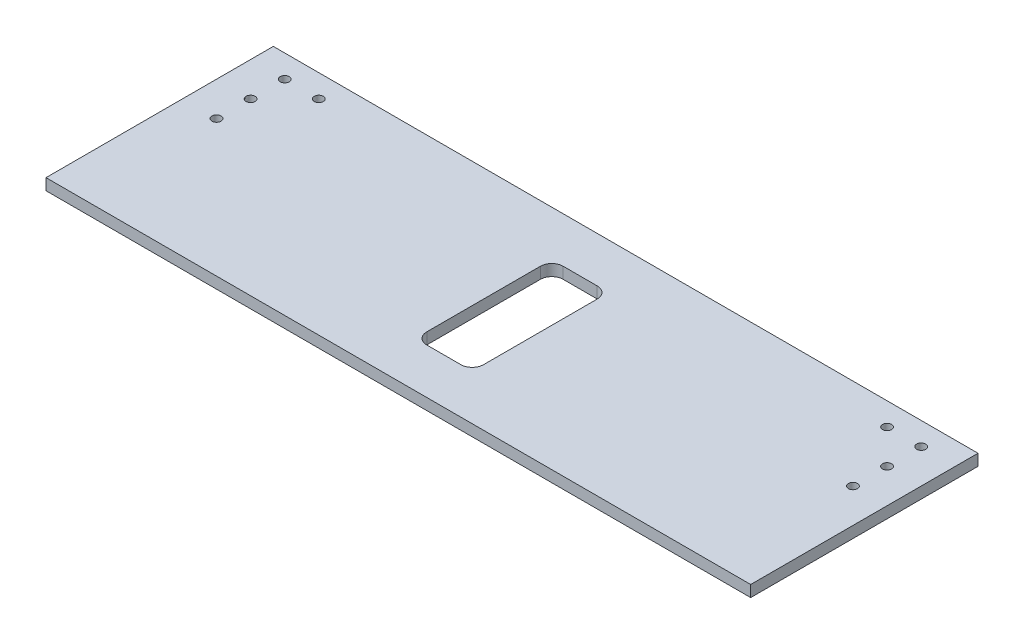
SolidWorks part; units mm, degrees
ref_plane "前视基准面" through (0, 0, 0) normal (0, 0, 1) x (1, 0, 0)
ref_plane "上视基准面" through (0, 0, 0) normal (0, 1, 0) x (1, 0, 0)
ref_plane "右视基准面" through (0, 0, 0) normal (1, 0, 0) x (0, 0, -1)
sketch "Sketch1" plane through (0, 0, 0) normal (0, 1, 0) x (1, 0, 0)
  line L0 (0, 50) -> (0, 97.5) construction
  line L1 (-155, 50) -> (155, 50)
  line L2 (-155, 50) -> (-155, -50)
  line L3 (-155, -50) -> (155, -50)
  line L4 (155, 50) -> (155, -50)
  line L5 (-155, 50) -> (155, -50) construction
  line L6 (-155, -50) -> (155, 50) construction
  line L8 (-60, 145) -> (60, 145)
  line L9 (-60, 145) -> (-60, 50)
  line L10 (-60, 50) -> (60, 50)
  line L11 (60, 145) -> (60, 50)
  line L12 (-60, 145) -> (60, 50) construction
  line L13 (-60, 50) -> (60, 145) construction
  point P0 (0, 0)
  dimension "D1" = 310
  dimension "100" = 100
  dimension "D2" = 120
  dimension "D3" = 95
extrude "Boss-Extrude1" add sketch "Sketch1" along normal blind 5 contours L11 L8 L9 L1 | L4 L1 L2 L3
sketch "Sketch2" plane through (0, 5, 0) normal (0, 1, 0) x (1, 0, 0)
  line L0 (-140, -50) -> (-140, 50) construction
  line L1 (-155, -50) -> (155, -50) construction
  line L2 (-155, 50) -> (-60, 50) construction
  line L3 (0, 0) -> (0, 145) construction
  line L4 (-60, 145) -> (60, 145) construction
  line L5 (-155, 50) -> (-155, -50) construction
  line L6 (-155, 40) -> (155, 40) construction
  line L7 (-12.5, -30) -> (12.5, -30)
  line L8 (-12.5, -30) -> (-12.5, 30)
  line L9 (-12.5, 30) -> (12.5, 30)
  line L10 (12.5, -30) -> (12.5, 30)
  line L11 (-12.5, -30) -> (12.5, 30) construction
  line L12 (-12.5, 30) -> (12.5, -30) construction
  line L13 (-50, 145) -> (-50, 40) construction
  line L14 (-60, 145) -> (-60, 50) construction
  line L15 (140, -50) -> (140, 50) construction
  line L16 (50, 145) -> (50, 40) construction
  circle A0 centre (-140, 40) radius 2
  circle A2 centre (-125, 40) radius 2
  circle A3 centre (-140, 25) radius 2
  circle A4 centre (-140, 10) radius 2
  circle A5 centre (140, 10) radius 2
  circle A6 centre (140, 25) radius 2
  circle A7 centre (125, 40) radius 2
  circle A8 centre (140, 40) radius 2
  circle A9 centre (-50, 130) radius 2
  circle A10 centre (50, 130) radius 2
  point P26 (0, 40)
  dimension "D6" = 4
  dimension "D7" = 15
  dimension "D8" = 15
  dimension "D9" = 15
  dimension "D10" = 15
  dimension "D11" = 4
  dimension "D1" = 15
  dimension "D2" = 25
  dimension "D3" = 20
  dimension "D4" = 10
  dimension "D5" = 10
extrude "Cut-Extrude1" cut sketch "Sketch2" against normal through all
fillet "Fillet1" radius 5 4 edges at (-12.5, 2.5, 30) (12.5, 2.5, -30) (12.5, 2.5, 30) (-12.5, 2.5, -30)
sketch "Sketch5" plane through (0, 5, 0) normal (0, 1, 0) x (1, 0, 0)
  line L0 (-60, 50) -> (60, 50) construction
  line L1 (0, 50) -> (0, 85) construction
  line L3 (-40, 120) -> (40, 120)
  line L4 (-40, 120) -> (-40, 50)
  line L5 (-40, 50) -> (40, 50)
  line L6 (40, 120) -> (40, 50)
  line L7 (-40, 120) -> (40, 50) construction
  line L8 (-40, 50) -> (40, 120) construction
  line L9 (-60, 145) -> (60, 145) construction
  dimension "D1" = 70
  dimension "D2" = 80
  dimension "D3" = 25
extrude "Cut-Extrude2" cut sketch "Sketch5" against normal blind 5 contours L4 L3 L6 L5
chamfer "Chamfer1" distance 20 angle 45 4 edges at (-40, 2.5, -50) (40, 2.5, -50) (40, 2.5, -120) (-40, 2.5, -120)
sketch "Sketch6" plane through (0, 5, 0) normal (0, 1, 0) x (1, 0, 0)
  line L0 (-60, 145) -> (60, 145) construction
  line L1 (60, 50) -> (155, 50)
  line L2 (60, 50) -> (60, 145)
  line L3 (60, 145) -> (155, 145)
  line L4 (155, 50) -> (155, 145)
  line L5 (155, 50) -> (155, -50) construction
  line L6 (0, 0) -> (0, 145) construction
  line L7 (-155, 50) -> (-155, 145)
  line L8 (-60, 145) -> (-155, 145)
  line L9 (-60, 50) -> (-60, 145)
  line L10 (-60, 50) -> (-155, 50)
extrude "Boss-Extrude2" add sketch "Sketch6" against normal blind 5
sketch "Sketch7" plane through (0, 5, 0) normal (0, 1, 0) x (1, 0, 0)
  line L0 (-155, 50) -> (155, 50)
  line L1 (-155, 145) -> (-155, -50) construction
  line L2 (155, 145) -> (155, -50) construction
  line L3 (-20, 50) -> (20, 50) construction
  line L4 (-155, 50) -> (-155, 145)
  line L5 (-155, 145) -> (155, 145)
  line L6 (155, 145) -> (155, 50)
extrude "Cut-Extrude3" cut sketch "Sketch7" against normal through all
